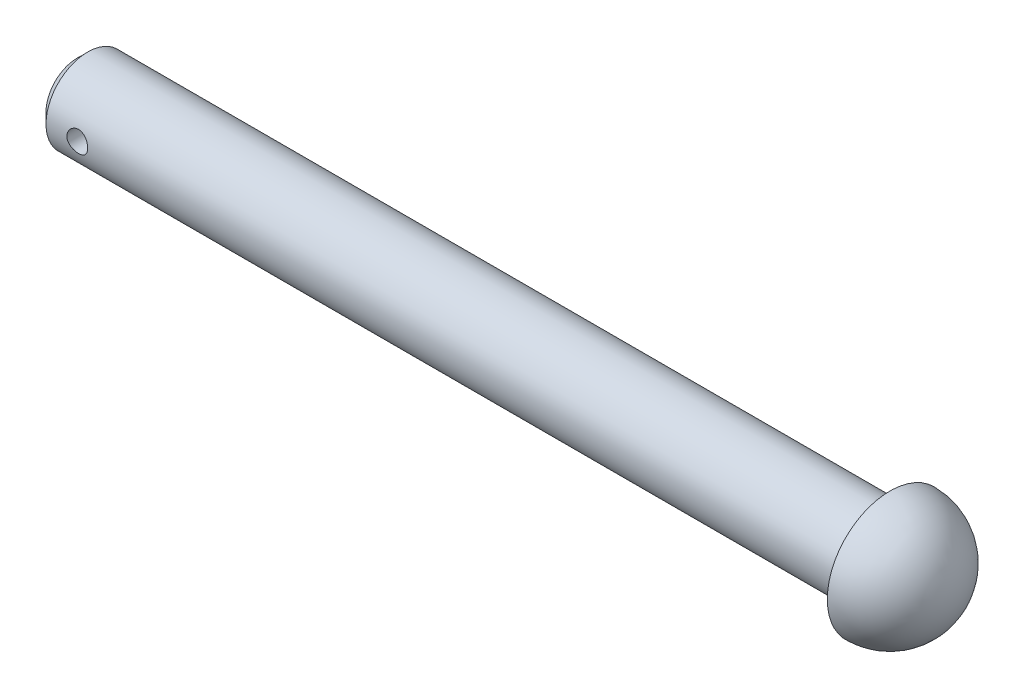
SolidWorks part; units mm, degrees
ref_plane "Front Plane" through (0, 0, 0) normal (0, 0, 1) x (1, 0, 0)
ref_plane "Top Plane" through (0, 0, 0) normal (0, 1, 0) x (1, 0, 0)
ref_plane "Right Plane" through (0, 0, 0) normal (1, 0, 0) x (0, 0, -1)
sketch "Sketch1" plane through (0, 0, 0) normal (0, 0, 1) x (1, 0, 0)
  line L0 (-20.4217, 0) -> (33.2169, 0) construction
  line L1 (-11.4922, 0) -> (-11.4922, -2)
  line L2 (-11.4922, -2) -> (27.5078, -2)
  line L4 (-11.4922, 0) -> (30.5078, 0)
  line L5 (27.5078, -2) -> (27.5078, -3)
  arc A1 (27.5078, -3) -> (30.5078, 0) centre (27.5078, 0) ccw
  dimension "D3" = 1
  dimension "D6" = 6
  dimension "D1" = 2
  dimension "D2" = 39
  dimension "D4" = 42
revolve "Revolve1" add sketch "Sketch1" angle 360 about L0
sketch "Sketch2" plane through (0, 0, 0) normal (0, 0, 1) x (1, 0, 0)
  line L0 (27.5078, 3) -> (27.5078, -3) construction
  line L1 (-11.4922, -2) -> (27.5078, -2) construction
  circle A0 centre (-9.4922, 0) radius 0.5
  point P6 (-21.7564, 10.3412)
  dimension "D1" = 1
  dimension "D2" = 37
  dimension "D3" = 2
extrude "Cut-Extrude1" cut sketch "Sketch2" against normal mid plane 10
chamfer "Chamfer1" distance 0.5 angle 45 1 edges at (-11.4922, 0, 2)
